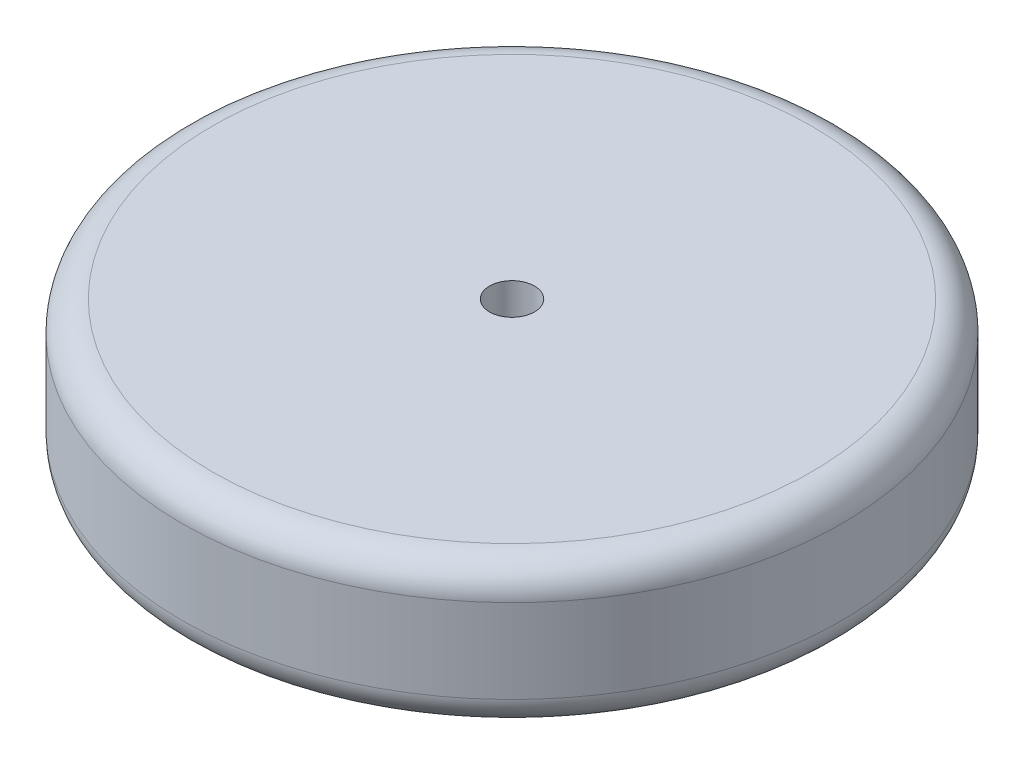
SolidWorks part; units mm, degrees
material "ALUMINUM 6061-T6"
ref_plane "Front Plane" through (0, 0, 0) normal (0, 0, 1) x (1, 0, 0)
ref_plane "Top Plane" through (0, 0, 0) normal (0, 1, 0) x (1, 0, 0)
ref_plane "Right Plane" through (0, 0, 0) normal (1, 0, 0) x (0, 0, -1)
sketch "Sketch1" plane through (0, 0, 0) normal (0, 1, 0) x (1, 0, 0)
  circle A0 centre (0, 0) radius 69.85
  dimension "D1" = 139.7
extrude "Boss-Extrude1" add sketch "Sketch1" along normal mid plane 30.48
sketch "Sketch2" plane through (0, 15.24, 0) normal (0, 1, 0) x (1, 0, 0)
  circle A0 centre (0, 0) radius 4.7625
  dimension "D1" = 9.525
extrude "Cut-Extrude1" cut sketch "Sketch2" against normal blind 30.48
fillet "Fillet1" radius 6.35 2 edges at (0, -15.24, 69.85) (0, 15.24, 69.85)
